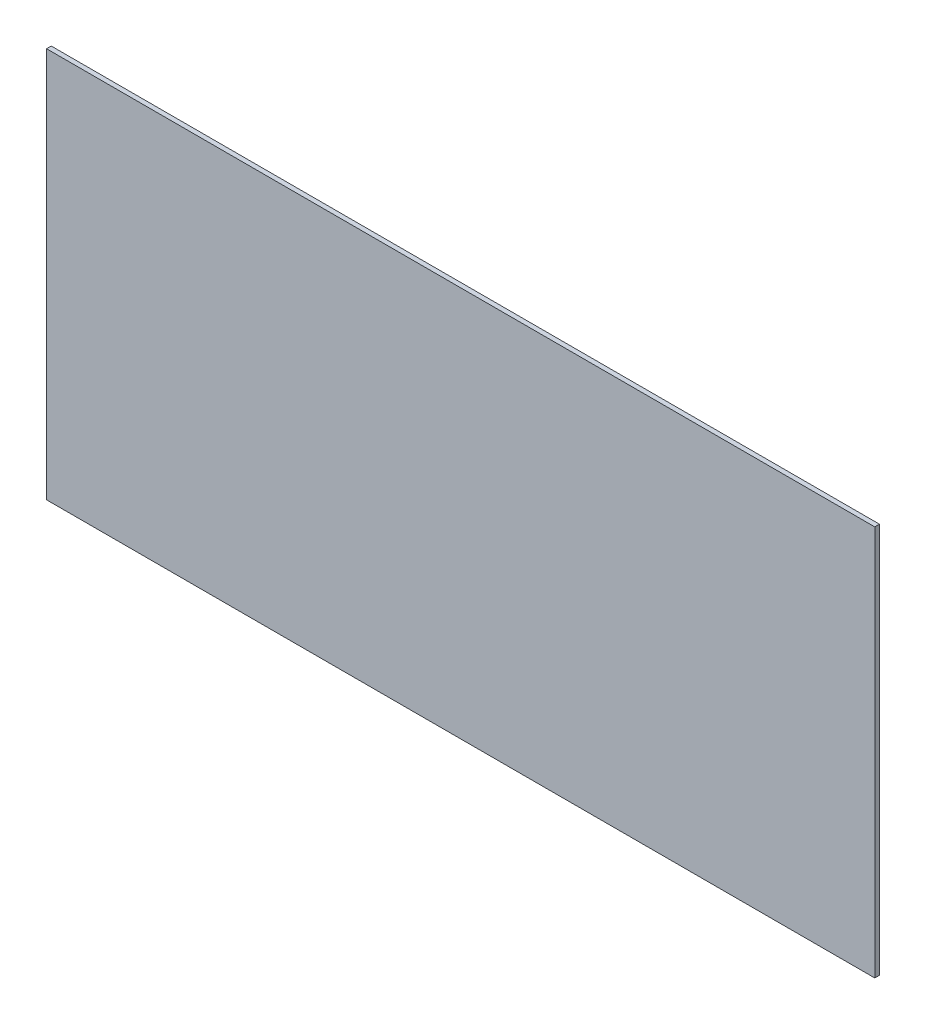
SolidWorks part; units mm, degrees
ref_plane "Plano frontal" through (0, 0, 0) normal (0, 0, 1) x (1, 0, 0)
ref_plane "Plano superior" through (0, 0, 0) normal (0, 1, 0) x (1, 0, 0)
ref_plane "Plano direito" through (0, 0, 0) normal (1, 0, 0) x (0, 0, -1)
sketch "Esboço1" plane through (0, 0, 0) normal (0, 0, 1) x (1, 0, 0)
  line L1 (-265, 125) -> (265, 125)
  line L2 (-265, 125) -> (-265, -125)
  line L3 (-265, -125) -> (265, -125)
  line L4 (265, 125) -> (265, -125)
  line L5 (-265, 125) -> (265, -125) construction
  line L6 (-265, -125) -> (265, 125) construction
  point P0 (0, 0)
  dimension "D1" = 250
  dimension "D2" = 530
extrude "Ressalto-extrusão1" add sketch "Esboço1" along normal blind 3
